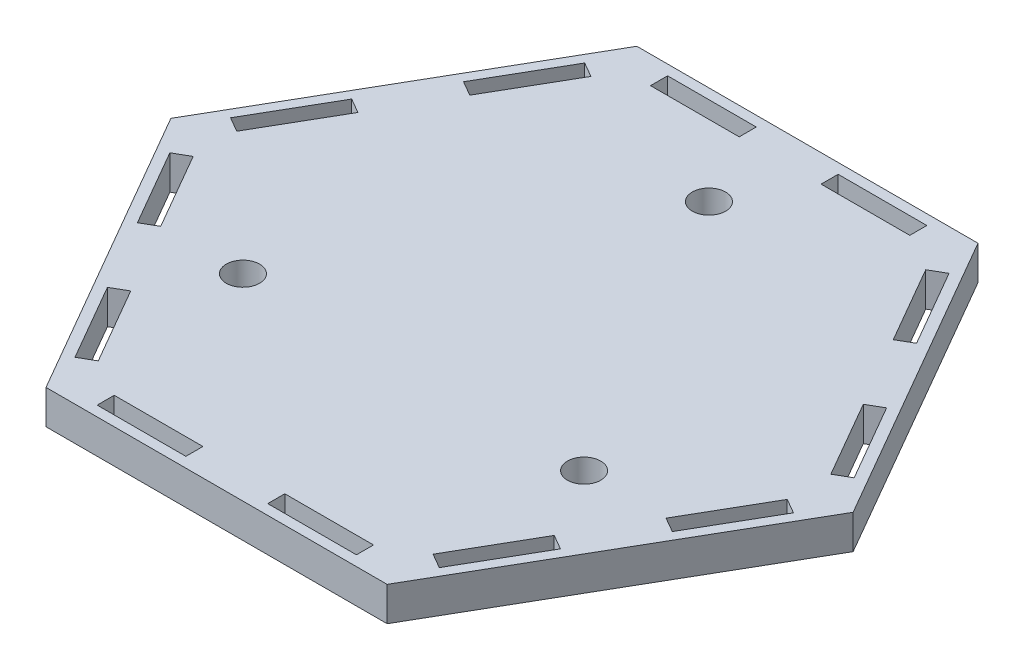
SolidWorks part; units mm, degrees
material "Cedar"
ref_plane "Front Plane" through (0, 0, 0) normal (0, 0, 1) x (1, 0, 0)
ref_plane "Top Plane" through (0, 0, 0) normal (0, 1, 0) x (1, 0, 0)
ref_plane "Right Plane" through (0, 0, 0) normal (1, 0, 0) x (0, 0, -1)
sketch "Sketch1" plane through (0, 0, 0) normal (0, 1, 0) x (1, 0, 0)
  line L0 (-63.5, 0) -> (-31.75, -54.9926)
  line L1 (63.5, 0) -> (31.75, 54.9926)
  line L2 (31.75, 54.9926) -> (-31.75, 54.9926)
  line L3 (-31.75, 54.9926) -> (-63.5, 0)
  line L4 (-31.75, -54.9926) -> (31.75, -54.9926)
  line L5 (31.75, -54.9926) -> (63.5, 0)
  line L6 (0, 0) -> (63.5, 0) construction
  circle A0 centre (0, 0) radius 54.9926 construction
  dimension "D1" = 63.5
extrude "Boss-Extrude1" add sketch "Sketch1" along normal blind 6.35
sketch "Sketch2" plane through (0, 6.35, 0) normal (0, 1, 0) x (1, 0, 0)
  line L0 (0, 0) -> (0, 36.6617) construction
  line L1 (31.75, -18.3309) -> (0, 36.6617) construction
  line L2 (0, 36.6617) -> (-31.75, -18.3309) construction
  line L3 (-31.75, -18.3309) -> (31.75, -18.3309) construction
  line L4 (-60.5671, 5.08) -> (-25.8841, -54.9926) construction
  line L5 (-31.75, 54.9926) -> (-63.5, 0) construction
  line L6 (-31.75, -54.9926) -> (31.75, -54.9926) construction
  line L7 (-63.5, 0) -> (-31.75, -54.9926) construction
  line L8 (-47.625, -27.4963) -> (-43.2256, -24.9563) construction
  line L9 (-55.2906, -4.0591) -> (-58.0402, -5.6466)
  line L10 (-58.0402, -5.6466) -> (-49.7852, -19.9447)
  line L11 (-49.7852, -19.9447) -> (-47.0356, -18.3572)
  line L12 (-47.0356, -18.3572) -> (-55.2906, -4.0591)
  line L13 (-31.1606, -45.8535) -> (-33.9102, -47.441)
  line L14 (-39.4156, -31.5554) -> (-31.1606, -45.8535)
  line L15 (-33.9102, -47.441) -> (-42.1652, -33.1429)
  line L16 (-42.1652, -33.1429) -> (-39.4156, -31.5554)
  line L17 (-25.8841, 54.9926) -> (-60.5671, -5.08) construction
  line L18 (-31.1606, 45.8535) -> (-33.9102, 47.441)
  line L19 (-33.9102, 47.441) -> (-42.1652, 33.1429)
  line L20 (-39.4156, 31.5554) -> (-31.1606, 45.8535)
  line L21 (-42.1652, 33.1429) -> (-39.4156, 31.5554)
  line L22 (-47.625, 27.4963) -> (-43.2256, 24.9563) construction
  line L23 (-49.7852, 19.9447) -> (-47.0356, 18.3572)
  line L24 (-58.0402, 5.6466) -> (-49.7852, 19.9447)
  line L25 (-47.0356, 18.3572) -> (-55.2906, 4.0591)
  line L26 (-55.2906, 4.0591) -> (-58.0402, 5.6466)
  line L27 (34.6829, 49.9126) -> (-34.6829, 49.9126) construction
  line L28 (24.13, 49.9126) -> (24.13, 53.0876)
  line L29 (24.13, 53.0876) -> (7.62, 53.0876)
  line L30 (7.62, 49.9126) -> (24.13, 49.9126)
  line L31 (7.62, 53.0876) -> (7.62, 49.9126)
  line L32 (0, 54.9926) -> (0, 49.9126) construction
  line L33 (-7.62, 53.0876) -> (-7.62, 49.9126)
  line L34 (-24.13, 53.0876) -> (-7.62, 53.0876)
  line L35 (-7.62, 49.9126) -> (-24.13, 49.9126)
  line L36 (-24.13, 49.9126) -> (-24.13, 53.0876)
  line L37 (60.5671, -5.08) -> (25.8841, 54.9926) construction
  line L38 (55.2906, 4.0591) -> (58.0402, 5.6466)
  line L39 (58.0402, 5.6466) -> (49.7852, 19.9447)
  line L40 (47.0356, 18.3572) -> (55.2906, 4.0591)
  line L41 (49.7852, 19.9447) -> (47.0356, 18.3572)
  line L42 (47.625, 27.4963) -> (43.2256, 24.9563) construction
  line L43 (42.1652, 33.1429) -> (39.4156, 31.5554)
  line L44 (33.9102, 47.441) -> (42.1652, 33.1429)
  line L45 (39.4156, 31.5554) -> (31.1606, 45.8535)
  line L46 (31.1606, 45.8535) -> (33.9102, 47.441)
  line L47 (25.8841, -54.9926) -> (60.5671, 5.08) construction
  line L48 (31.1606, -45.8535) -> (33.9102, -47.441)
  line L49 (33.9102, -47.441) -> (42.1652, -33.1429)
  line L50 (39.4156, -31.5554) -> (31.1606, -45.8535)
  line L51 (42.1652, -33.1429) -> (39.4156, -31.5554)
  line L52 (47.625, -27.4963) -> (43.2256, -24.9563) construction
  line L53 (49.7852, -19.9447) -> (47.0356, -18.3572)
  line L54 (58.0402, -5.6466) -> (49.7852, -19.9447)
  line L55 (47.0356, -18.3572) -> (55.2906, -4.0591)
  line L56 (55.2906, -4.0591) -> (58.0402, -5.6466)
  line L57 (-34.6829, -49.9126) -> (34.6829, -49.9126) construction
  line L58 (-24.13, -49.9126) -> (-24.13, -53.0876)
  line L59 (-24.13, -53.0876) -> (-7.62, -53.0876)
  line L60 (-7.62, -49.9126) -> (-24.13, -49.9126)
  line L61 (-7.62, -53.0876) -> (-7.62, -49.9126)
  line L62 (0, -54.9926) -> (0, -49.9126) construction
  line L63 (7.62, -53.0876) -> (7.62, -49.9126)
  line L64 (24.13, -53.0876) -> (7.62, -53.0876)
  line L65 (7.62, -49.9126) -> (24.13, -49.9126)
  line L66 (24.13, -49.9126) -> (24.13, -53.0876)
  circle A0 centre (0, 0) radius 18.3309 construction
  circle A1 centre (-31.75, -18.3309) radius 3.0988
  circle A4 centre (0, 36.6617) radius 3.0988
  circle A5 centre (31.75, -18.3309) radius 3.0988
  point P13 (0, 0)
  point P92 (0, 0)
  point P94 (0, 0)
  dimension "D2" = 6.1976
  dimension "D3" = 3
  dimension "D1" = 63.5
  dimension "D4" = 5.08
  dimension "D5" = 3.175
  dimension "D6" = 16.51
  dimension "D7" = 7.62
  dimension "D8" = 6
extrude "Cut-Extrude1" cut sketch "Sketch2" against normal through all
